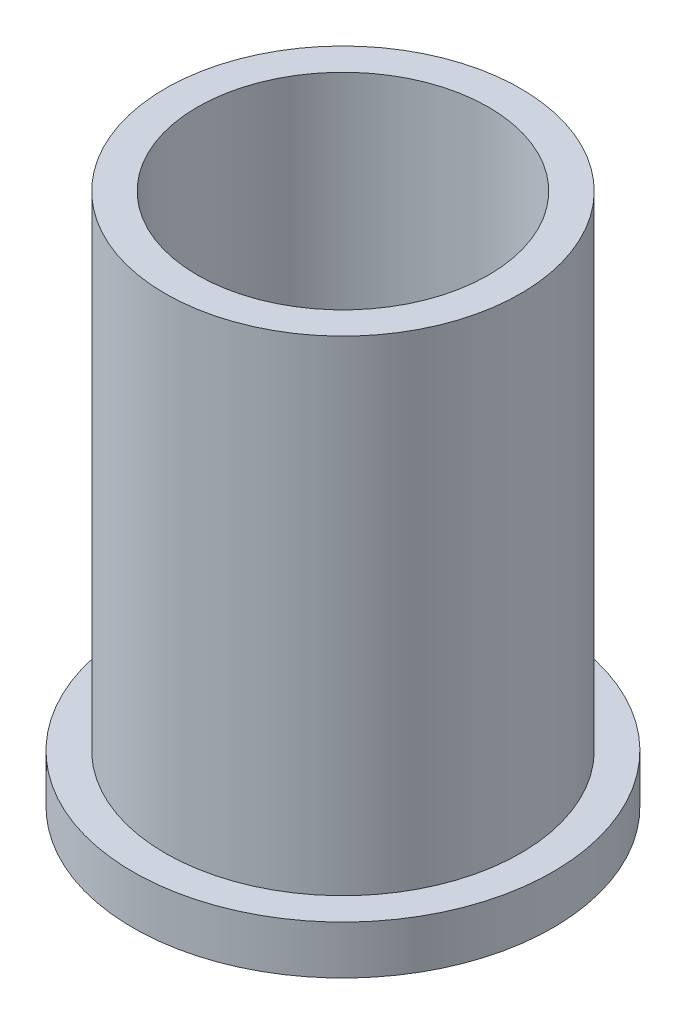
SolidWorks part; units mm, degrees
ref_plane "Front Plane" through (0, 0, 0) normal (0, 0, 1) x (1, 0, 0)
ref_plane "Top Plane" through (0, 0, 0) normal (0, 1, 0) x (1, 0, 0)
ref_plane "Right Plane" through (0, 0, 0) normal (1, 0, 0) x (0, 0, -1)
sketch "Sketch1" plane through (0, 0, 0) normal (0, 1, 0) x (1, 0, 0)
  circle A0 centre (0, 0) radius 45.05
  circle A1 centre (0, 0) radius 55
  dimension "D1" = 90.1
  dimension "D2" = 110
extrude "Boss-Extrude1" add sketch "Sketch1" along normal blind 150
sketch "Sketch2" plane through (0, 0, 0) normal (0, -1, 0) x (1, 0, 0)
  circle A0 centre (0, 0) radius 65
  dimension "D1" = 130
extrude "Boss-Extrude2" add sketch "Sketch2" along normal blind 15
